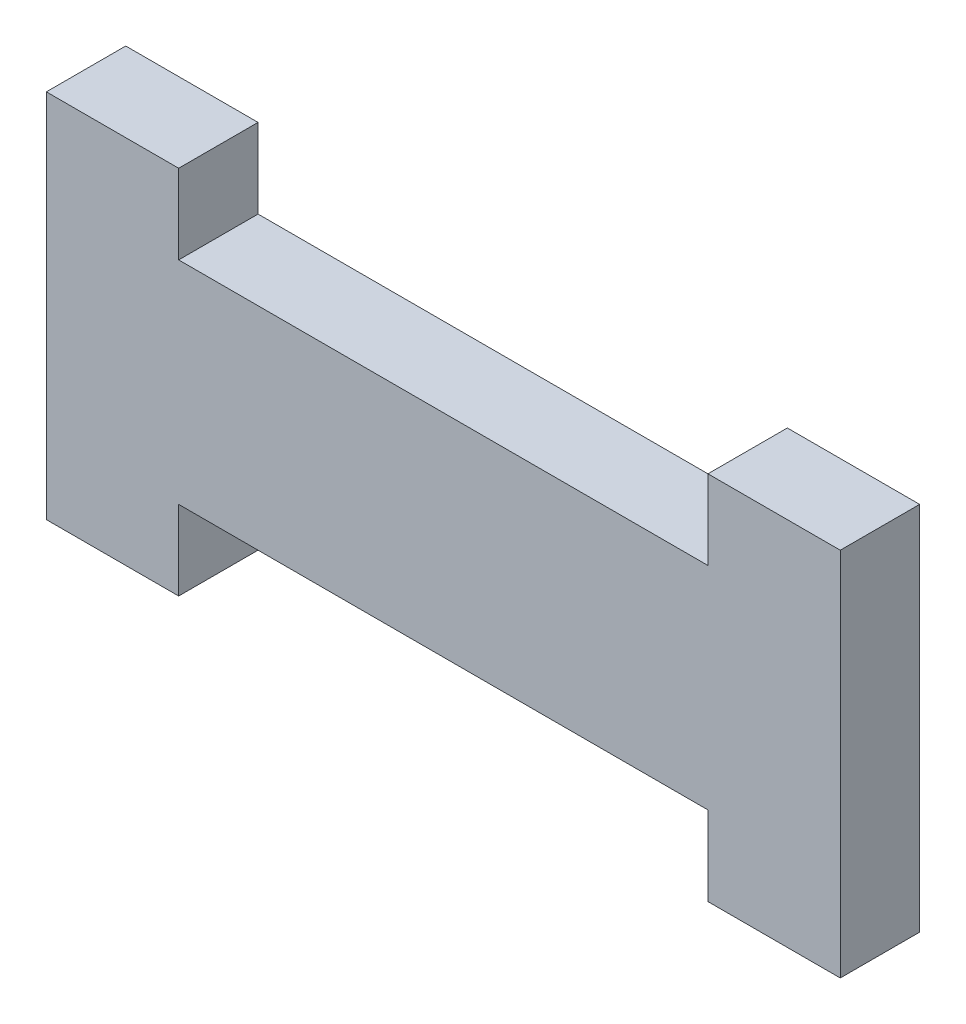
SolidWorks part; units mm, degrees
material "Acrylic (Medium-high impact)"
ref_plane "Front Plane" through (0, 0, 0) normal (0, 0, 1) x (1, 0, 0)
ref_plane "Top Plane" through (0, 0, 0) normal (0, 1, 0) x (1, 0, 0)
ref_plane "Right Plane" through (0, 0, 0) normal (1, 0, 0) x (0, 0, -1)
sketch "Sketch1" plane through (0, 0, 0) normal (0, 0, 1) x (1, 0, 0)
  line L0 (0, 14) -> (60, 14) construction
  line L1 (0, 0) -> (10, 0)
  line L2 (0, 0) -> (0, 28)
  line L3 (0, 28) -> (10, 28)
  line L4 (60, 0) -> (60, 28)
  line L6 (10, 0) -> (10, 6)
  line L7 (10, 6) -> (50, 6)
  line L8 (50, 0) -> (50, 6)
  line L9 (10, 22) -> (50, 22)
  line L10 (50, 28) -> (50, 22)
  line L12 (10, 28) -> (10, 22)
  line L13 (50, 28) -> (60, 28)
  line L14 (50, 0) -> (60, 0)
  dimension "D1" = 16
  dimension "D2" = 60
  dimension "D3" = 10
  dimension "D4" = 10
  dimension "D5" = 6
extrude "Boss-Extrude1" add sketch "Sketch1" along normal blind 6
